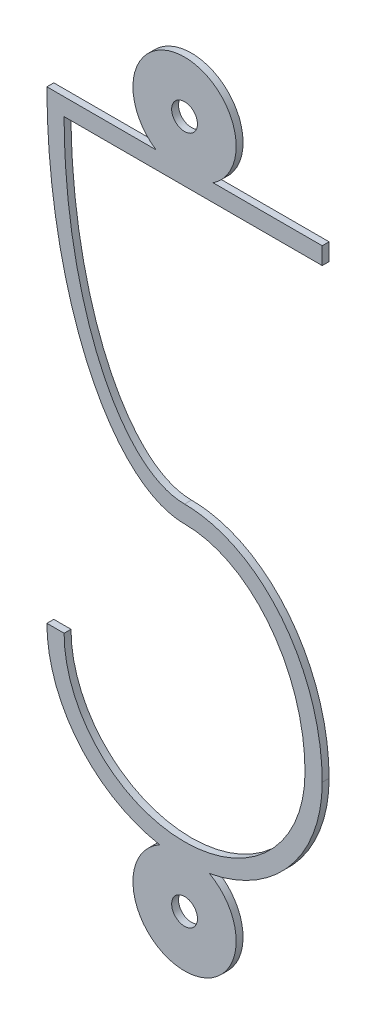
SolidWorks part; units mm, degrees
material "3.0517 (EN-AW 3003)"
ref_plane "Front Plane" through (0, 0, 0) normal (0, 0, 1) x (1, 0, 0)
ref_plane "Top Plane" through (0, 0, 0) normal (0, 1, 0) x (1, 0, 0)
ref_plane "Right Plane" through (0, 0, 0) normal (1, 0, 0) x (0, 0, -1)
sketch "Sketch1" plane through (0, 0, 0) normal (0, 0, 1) x (1, 0, 0)
  line L0 (0, -10) -> (0, 10) construction
  line L10 (4, -8.75) -> (4, -4.75) construction
  line L11 (-4, -8.75) -> (-4, -4.75) construction
  line L12 (-4, -8.75) -> (4, -8.75) construction
  line L13 (0, -0.25) -> (0, 0.25) construction
  line L14 (-4, -4.75) -> (-3.5, -4.75)
  line L15 (0.8292, 8.75) -> (4, 8.75)
  line L16 (4, 8.25) -> (-3.5, 8.25)
  line L17 (4, 8.75) -> (4, 8.25)
  line L18 (-4, 8.75) -> (-0.8292, 8.75)
  arc A0 (-0.7208, -8.6845) -> (0.7208, -8.6845) centre (0, -10) ccw
  circle A1 centre (0, -10) radius 0.375
  arc A2 (0.8292, 8.75) -> (-0.8292, 8.75) centre (0, 10) ccw
  circle A3 centre (0, 10) radius 0.375
  arc A5 (3.5, -4.75) -> (-3.5, -4.75) centre (0, -4.75) cw
  arc A7 (0.7208, -8.6845) -> (4, -4.75) centre (0, -4.75) ccw
  arc A8 (-4, -4.75) -> (-0.7208, -8.6845) centre (0, -4.75) ccw
  ellipse E0 centre (0, 8.25) end of major axis (0, 16.25) minor radius 3.5 (0, 0.25) -> (-3.5, 8.25) cw
  ellipse E3 centre (0, -4.75) end of major axis (0, -0.25) minor radius 3.5 (0, -0.25) -> (3.5, -4.75) cw
  ellipse E4 centre (0, -4.75) end of major axis (0, 0.25) minor radius 4 (0, 0.25) -> (4, -4.75) cw
  ellipse E5 centre (0, 8.75) end of major axis (0, -0.25) minor radius 4 (0, -0.25) -> (-4, 8.75) cw
  dimension "D2" = 3
  dimension "D3" = 0.75
  dimension "D4" = 1.25
  dimension "D5" = 8
  dimension "D7" = 0.5
  dimension "D8" = 1.25
  dimension "D1" = 20
  dimension "D6" = 0.5
  dimension "D10" = 0.5
  dimension "D9" = 0.5
extrude "Boss-Extrude1" add sketch "Sketch1" along normal mid plane 0.2
sketch "Sketch2" plane through (0, 0, 0) normal (0, 0, 1) x (1, 0, 0)
  line L10 (-3.2404, -4.5) -> (-4.2426, -4.5)
  line L11 (-3.2483, 8) -> (4.25, 8)
  line L12 (4.25, 8) -> (4.25, 9)
  line L13 (4.25, 9) -> (1.4361, 9)
  line L14 (-1.4361, 9) -> (-4.2485, 9)
  line L15 (-3.2404, -4.5) -> (-4.2426, -4.5)
  line L16 (-3.2483, 8) -> (4.25, 8)
  line L17 (4.25, 8) -> (4.25, 9)
  line L18 (4.25, 9) -> (0, 9)
  line L19 (0, 9) -> (-4.2485, 9)
  arc A10 (-3.2404, -4.5) -> (3.25, -4.75) centre (0, -4.75) ccw
  arc A11 (-4.2426, -4.5) -> (-1.2771, -8.8036) centre (0, -4.75) ccw
  arc A12 (-1.2771, -8.8036) -> (1.2771, -8.8036) centre (0, -10) ccw
  arc A13 (1.2771, -8.8036) -> (4.25, -4.75) centre (0, -4.75) ccw
  arc A14 (1.4361, 9) -> (-1.4361, 9) centre (0, 10) ccw
  arc A15 (-3.2404, -4.5) -> (3.25, -4.75) centre (0, -4.75) ccw
  arc A16 (-4.2426, -4.5) -> (0, -9) centre (0, -4.75) ccw
  arc A18 (0, -9) -> (4.25, -4.75) centre (0, -4.75) ccw
  spline S0 degree 3 poles (-2983.1654, -140.0127) (976.8038, 399.7989) (-18.647, 119.4231) (-3.9725, 5.2999) (-3.79, 4.3937) (-3.3732, 3.058) (-3.2085, 2.6136) (-2.9133, 1.9697) (-2.807, 1.7591) (-2.5746, 1.3477) (-2.4481, 1.1465) (-2.1738, 0.7639) (-2.0257, 0.5816) (-1.6997, 0.2416) (-1.52, 0.0828) (-1.2295, -0.1197) (-1.129, -0.1815) (-0.919, -0.2916) (-0.8092, -0.3399) (13.0251, -5.1841) (75.0168, 122.7293) (-1976.001, 2252.2366) knots -30.615764 -30.615764 -30.615764 -30.615764 0.25 0.25 0.5 0.5 0.625 0.625 0.6875 0.6875 0.75 0.75 0.8125 0.8125 0.875 0.875 0.90625 0.90625 0.9375 0.9375 4.784859 4.784859 4.784859 4.784859 only from (-4.2485, 9) to (0, -0.5)
  spline S1 degree 3 poles (-588.2534, -2941.8307) (-91.4705, -266.921) (-20.6156, 5.8482) (0.8476, -0.6447) (0.9646, -0.6895) (1.1889, -0.7928) (1.297, -0.8517) (1.6106, -1.0484) (1.8049, -1.2068) (2.1512, -1.5547) (2.306, -1.7461) (2.7205, -2.3648) (2.9175, -2.813) (14.4962, -44.0459) (-478.3179, -173.0898) (1052.567, 2783.0186) knots -11.141825 -11.141825 -11.141825 -11.141825 0.125 0.125 0.1875 0.1875 0.25 0.25 0.375 0.375 0.5 0.5 0.75 0.75 22.134316 22.134316 22.134316 22.134316 only from (0, -0.5) to (3.25, -4.75)
  spline S2 degree 3 poles (2982.7363, 284.63) (-1215.6796, -357.7204) (25.0686, -72.7516) (3.8915, -2.6137) (3.7773, -2.3194) (3.5053, -1.761) (3.3469, -1.4941) (2.9792, -0.9882) (2.7707, -0.7513) (2.4277, -0.4355) (2.308, -0.3362) (2.0566, -0.1506) (1.924, -0.0639) (1.5168, 0.169) (1.2317, 0.2896) (-15.9151, 5.0376) (-83.6431, -112.3388) (2669.039, -1362.048) knots -28.990637 -28.990637 -28.990637 -28.990637 0.25 0.25 0.375 0.375 0.5 0.5 0.625 0.625 0.6875 0.6875 0.75 0.75 0.875 0.875 7.897187 7.897187 7.897187 7.897187 only from (4.25, -4.75) to (0, 0.5)
  spline S3 degree 3 poles (-1116.3037, 2783.0517) (60.6277, 105.4259) (9.8532, -3.7615) (-0.707, 0.6843) (-0.8616, 0.7829) (-1.1497, 1.0147) (-1.2785, 1.1443) (-1.5164, 1.421) (-1.6257, 1.5688) (-1.9289, 2.0287) (-2.0959, 2.3517) (-2.388, 3.0171) (-2.5126, 3.3609) (-2.8361, 4.4082) (-2.9831, 5.1168) (-13.4104, 79.1198) (473.7379, 227.6362) (-2988.4678, -221.0756) knots -3.756657 -3.756657 -3.756657 -3.756657 0.0625 0.0625 0.125 0.125 0.1875 0.1875 0.25 0.25 0.375 0.375 0.5 0.5 0.75 0.75 26.354562 26.354562 26.354562 26.354562 only from (0, 0.5) to (-3.2483, 8)
  spline S4 degree 3 poles (-4.2485, 9) (-4.2599, 8.0617) (-4.2083, 7.1338) (-3.9725, 5.2999) (-3.79, 4.3937) (-3.3732, 3.058) (-3.2085, 2.6136) (-2.9133, 1.9697) (-2.807, 1.7591) (-2.5746, 1.3477) (-2.4481, 1.1465) (-2.1738, 0.7639) (-2.0257, 0.5816) (-1.6997, 0.2416) (-1.52, 0.0828) (-1.2295, -0.1197) (-1.129, -0.1815) (-0.919, -0.2916) (-0.8092, -0.3399) (-0.4748, -0.457) (-0.2391, -0.5) (0, -0.5) knots 0 0 0 0 0.25 0.25 0.5 0.5 0.625 0.625 0.6875 0.6875 0.75 0.75 0.8125 0.8125 0.875 0.875 0.90625 0.90625 0.9375 0.9375 1 1 1 1
  spline S5 degree 3 poles (0, -0.5) (0.2495, -0.5) (0.4924, -0.5373) (0.8476, -0.6447) (0.9646, -0.6895) (1.1889, -0.7928) (1.297, -0.8517) (1.6106, -1.0484) (1.8049, -1.2068) (2.1512, -1.5547) (2.306, -1.7461) (2.7205, -2.3648) (2.9175, -2.813) (3.1851, -3.7659) (3.25, -4.2545) (3.25, -4.75) knots 0 0 0 0 0.125 0.125 0.1875 0.1875 0.25 0.25 0.375 0.375 0.5 0.5 0.75 0.75 1 1 1 1
  spline S6 degree 3 poles (4.25, -4.75) (4.25, -4.1222) (4.162, -3.5093) (3.8915, -2.6137) (3.7773, -2.3194) (3.5053, -1.761) (3.3469, -1.4941) (2.9792, -0.9882) (2.7707, -0.7513) (2.4277, -0.4355) (2.308, -0.3362) (2.0566, -0.1506) (1.924, -0.0639) (1.5168, 0.169) (1.2317, 0.2896) (0.6319, 0.4556) (0.3159, 0.5) (0, 0.5) knots 0 0 0 0 0.25 0.25 0.375 0.375 0.5 0.5 0.625 0.625 0.6875 0.6875 0.75 0.75 0.875 0.875 1 1 1 1
  spline S7 degree 3 poles (0, 0.5) (-0.1861, 0.5) (-0.367, 0.5412) (-0.707, 0.6843) (-0.8616, 0.7829) (-1.1497, 1.0147) (-1.2785, 1.1443) (-1.5164, 1.421) (-1.6257, 1.5688) (-1.9289, 2.0287) (-2.0959, 2.3517) (-2.388, 3.0171) (-2.5126, 3.3609) (-2.8361, 4.4082) (-2.9831, 5.1168) (-3.1848, 6.548) (-3.2382, 7.2707) (-3.2483, 8) knots 0 0 0 0 0.0625 0.0625 0.125 0.125 0.1875 0.1875 0.25 0.25 0.375 0.375 0.5 0.5 0.75 0.75 1 1 1 1
  dimension "D1" = 0.25
extrude "Boss-Extrude2" [suppressed] add sketch "Sketch2" along normal mid plane 0.6
